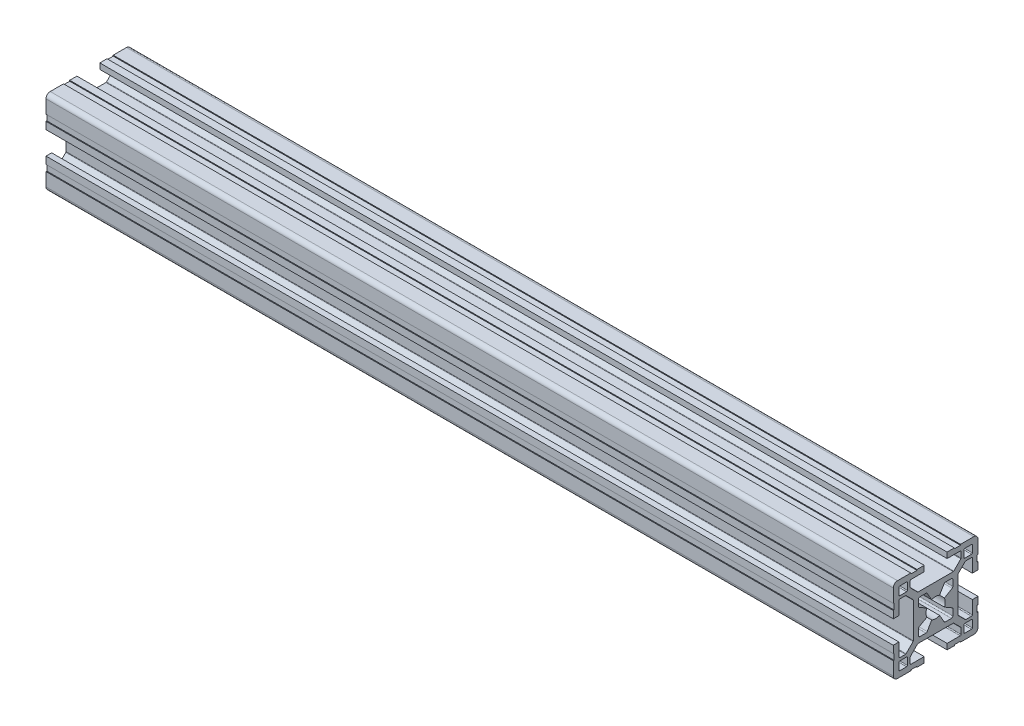
SolidWorks part; units mm, degrees
material "6063-T5"
ref_plane "Plano frontal" through (0, 0, 0) normal (0, 0, 1) x (1, 0, 0)
ref_plane "Plano superior" through (0, 0, 0) normal (0, 1, 0) x (1, 0, 0)
ref_plane "Plano direito" through (0, 0, 0) normal (1, 0, 0) x (0, 0, -1)
sketch "Esboço1" plane through (0, 0, 0) normal (0, 0, 1) x (1, 0, 0)
  line L0 (0, 0) -> (300, 0)
  point P3 (150, 0)
  dimension "D1" = 300
other "Quadrado PF30-11 - PERFIL 3030 CENTRO M8(1)"
ref_plane "Plano1" through (0, 0, 0) normal (1, 0, 0) x (0, 1, 0)
sketch "Sketch1" plane through (0, 0, 0) normal (1, 0, 0) x (0, 1, 0)
  line L0 (-6.1, -3.4254) -> (-6.1, -5.6)
  line L1 (-5.6, -6.1) -> (-3.4254, -6.1)
  line L2 (3.4254, -6.1) -> (5.6, -6.1)
  line L3 (6.1, -5.6) -> (6.1, -3.4254)
  line L4 (6.1, 3.4254) -> (6.1, 5.6)
  line L5 (5.6, 6.1) -> (3.4254, 6.1)
  line L6 (-3.4254, 6.1) -> (-5.6, 6.1)
  line L7 (-6.1, 5.6) -> (-6.1, 3.4254)
  line L8 (15, 6.6) -> (14.7, 6.6)
  line L9 (5.85, -2.9924) -> (3.097, -1.403)
  line L10 (10, 12.7) -> (10, 10.3)
  line L11 (13, -12.7) -> (13, -10.3)
  line L12 (-10.3, -10) -> (-12.7, -10)
  line L13 (-13, 12.7) -> (-13, 10.3)
  line L14 (3.097, 1.403) -> (5.85, 2.9924)
  line L15 (2.9924, 5.85) -> (1.403, 3.097)
  line L16 (-1.403, 3.097) -> (-2.9924, 5.85)
  line L17 (-5.85, 2.9924) -> (-3.097, 1.403)
  line L18 (-3.097, -1.403) -> (-5.85, -2.9924)
  line L19 (-2.9924, -5.85) -> (-1.403, -3.097)
  line L20 (1.403, -3.097) -> (2.9924, -5.85)
  line L21 (10.3, 10) -> (12.7, 10)
  line L22 (13, 10.3) -> (13, 12.7)
  line L23 (12.7, 13) -> (10.3, 13)
  line L24 (12.7, -10) -> (10.3, -10)
  line L25 (10, -10.3) -> (10, -12.7)
  line L26 (10.3, -13) -> (12.7, -13)
  line L27 (-13, -10.3) -> (-13, -12.7)
  line L28 (-12.7, -13) -> (-10.3, -13)
  line L29 (-10, -12.7) -> (-10, -10.3)
  line L30 (-12.7, 10) -> (-10.3, 10)
  line L31 (-10, 10.3) -> (-10, 12.7)
  line L32 (-10.3, 13) -> (-12.7, 13)
  line L33 (15, 4.05) -> (15, 6.6)
  line L34 (13, 4.05) -> (15, 4.05)
  line L35 (13, 8.7) -> (13, 4.05)
  line L36 (10.6799, 9) -> (12.7, 9)
  line L37 (7.9879, 6.4322) -> (10.4678, 8.9121)
  line L38 (7.9, -6.2201) -> (7.9, 6.2201)
  line L39 (10.4678, -8.9121) -> (7.9879, -6.4322)
  line L40 (12.7, -9) -> (10.6799, -9)
  line L41 (13, -4.05) -> (13, -8.7)
  line L42 (15, -4.05) -> (13, -4.05)
  line L43 (15, -6.6) -> (15, -4.05)
  line L44 (14.7, -6.6) -> (15, -6.6)
  line L45 (14.7, -8.8) -> (14.7, -6.6)
  line L46 (15, -8.8) -> (14.7, -8.8)
  line L47 (15, -13.5) -> (15, -8.8)
  line L48 (8.8, -15) -> (13.5, -15)
  line L49 (8.8, -14.7) -> (8.8, -15)
  line L50 (6.6, -14.7) -> (8.8, -14.7)
  line L51 (6.6, -15) -> (6.6, -14.7)
  line L52 (4.05, -15) -> (6.6, -15)
  line L53 (4.05, -13) -> (4.05, -15)
  line L54 (8.7, -13) -> (4.05, -13)
  line L55 (9, -10.6799) -> (9, -12.7)
  line L56 (6.4322, -7.9879) -> (8.9121, -10.4678)
  line L57 (-6.2201, -7.9) -> (6.2201, -7.9)
  line L58 (-8.9121, -10.4678) -> (-6.4322, -7.9879)
  line L59 (-9, -12.7) -> (-9, -10.6799)
  line L60 (-4.05, -13) -> (-8.7, -13)
  line L61 (-4.05, -15) -> (-4.05, -13)
  line L62 (-6.6, -15) -> (-4.05, -15)
  line L63 (-6.6, -14.7) -> (-6.6, -15)
  line L64 (-8.8, -14.7) -> (-6.6, -14.7)
  line L65 (-8.8, -15) -> (-8.8, -14.7)
  line L66 (-13.5, -15) -> (-8.8, -15)
  line L67 (-15, -8.8) -> (-15, -13.5)
  line L68 (-14.7, -8.8) -> (-15, -8.8)
  line L69 (-14.7, -6.6) -> (-14.7, -8.8)
  line L70 (-15, -6.6) -> (-14.7, -6.6)
  line L71 (-15, -4.05) -> (-15, -6.6)
  line L72 (-13, -4.05) -> (-15, -4.05)
  line L73 (-13, -8.7) -> (-13, -4.05)
  line L74 (-10.6799, -9) -> (-12.7, -9)
  line L75 (-7.9879, -6.4322) -> (-10.4678, -8.9121)
  line L76 (-7.9, 6.2201) -> (-7.9, -6.2201)
  line L77 (-10.4678, 8.9121) -> (-7.9879, 6.4322)
  line L78 (-12.7, 9) -> (-10.6799, 9)
  line L79 (-13, 4.05) -> (-13, 8.7)
  line L80 (-15, 4.05) -> (-13, 4.05)
  line L81 (-15, 6.6) -> (-15, 4.05)
  line L82 (-14.7, 6.6) -> (-15, 6.6)
  line L83 (-14.7, 8.8) -> (-14.7, 6.6)
  line L84 (-15, 8.8) -> (-14.7, 8.8)
  line L85 (-15, 13.5) -> (-15, 8.8)
  line L86 (-8.8, 15) -> (-13.5, 15)
  line L87 (-8.8, 14.7) -> (-8.8, 15)
  line L88 (-6.6, 14.7) -> (-8.8, 14.7)
  line L89 (-6.6, 15) -> (-6.6, 14.7)
  line L90 (-4.05, 15) -> (-6.6, 15)
  line L91 (-4.05, 13) -> (-4.05, 15)
  line L92 (-8.7, 13) -> (-4.05, 13)
  line L93 (-9, 10.6799) -> (-9, 12.7)
  line L94 (-6.4322, 7.9879) -> (-8.9121, 10.4678)
  line L95 (6.2201, 7.9) -> (-6.2201, 7.9)
  line L96 (8.9121, 10.4678) -> (6.4322, 7.9879)
  line L97 (9, 12.7) -> (9, 10.6799)
  line L98 (4.05, 13) -> (8.7, 13)
  line L99 (4.05, 15) -> (4.05, 13)
  line L100 (6.6, 15) -> (4.05, 15)
  line L101 (6.6, 14.7) -> (6.6, 15)
  line L102 (8.8, 14.7) -> (6.6, 14.7)
  line L103 (8.8, 15) -> (8.8, 14.7)
  line L104 (13.5, 15) -> (8.8, 15)
  line L105 (15, 8.8) -> (15, 13.5)
  line L106 (14.7, 8.8) -> (15, 8.8)
  line L107 (14.7, 6.6) -> (14.7, 8.8)
  arc A0 (-5.85, -2.9924) -> (-6.1, -3.4254) centre (-5.6, -3.4254) ccw
  arc A1 (-6.1, -5.6) -> (-5.6, -6.1) centre (-5.6, -5.6) ccw
  arc A2 (-3.4254, -6.1) -> (-2.9924, -5.85) centre (-3.4254, -5.6) ccw
  arc A3 (2.9924, -5.85) -> (3.4254, -6.1) centre (3.4254, -5.6) ccw
  arc A4 (5.6, -6.1) -> (6.1, -5.6) centre (5.6, -5.6) ccw
  arc A5 (6.1, -3.4254) -> (5.85, -2.9924) centre (5.6, -3.4254) ccw
  arc A6 (5.85, 2.9924) -> (6.1, 3.4254) centre (5.6, 3.4254) ccw
  arc A7 (6.1, 5.6) -> (5.6, 6.1) centre (5.6, 5.6) ccw
  arc A8 (3.4254, 6.1) -> (2.9924, 5.85) centre (3.4254, 5.6) ccw
  arc A9 (-2.9924, 5.85) -> (-3.4254, 6.1) centre (-3.4254, 5.6) ccw
  arc A10 (-5.6, 6.1) -> (-6.1, 5.6) centre (-5.6, 5.6) ccw
  arc A11 (-6.1, 3.4254) -> (-5.85, 2.9924) centre (-5.6, 3.4254) ccw
  arc A12 (3.097, -1.403) -> (3.097, 1.403) centre (0, 0) ccw
  arc A13 (1.403, 3.097) -> (-1.403, 3.097) centre (0, 0) ccw
  arc A14 (-3.097, 1.403) -> (-3.097, -1.403) centre (0, 0) ccw
  arc A15 (-1.403, -3.097) -> (1.403, -3.097) centre (0, 0) ccw
  arc A16 (10, 10.3) -> (10.3, 10) centre (10.3, 10.3) ccw
  arc A17 (12.7, 10) -> (13, 10.3) centre (12.7, 10.3) ccw
  arc A18 (13, 12.7) -> (12.7, 13) centre (12.7, 12.7) ccw
  arc A19 (10.3, 13) -> (10, 12.7) centre (10.3, 12.7) ccw
  arc A20 (13, -10.3) -> (12.7, -10) centre (12.7, -10.3) ccw
  arc A21 (10.3, -10) -> (10, -10.3) centre (10.3, -10.3) ccw
  arc A22 (10, -12.7) -> (10.3, -13) centre (10.3, -12.7) ccw
  arc A23 (12.7, -13) -> (13, -12.7) centre (12.7, -12.7) ccw
  arc A24 (-12.7, -10) -> (-13, -10.3) centre (-12.7, -10.3) ccw
  arc A25 (-13, -12.7) -> (-12.7, -13) centre (-12.7, -12.7) ccw
  arc A26 (-10.3, -13) -> (-10, -12.7) centre (-10.3, -12.7) ccw
  arc A27 (-10, -10.3) -> (-10.3, -10) centre (-10.3, -10.3) ccw
  arc A28 (-13, 10.3) -> (-12.7, 10) centre (-12.7, 10.3) ccw
  arc A29 (-10.3, 10) -> (-10, 10.3) centre (-10.3, 10.3) ccw
  arc A30 (-10, 12.7) -> (-10.3, 13) centre (-10.3, 12.7) ccw
  arc A31 (-12.7, 13) -> (-13, 12.7) centre (-12.7, 12.7) ccw
  arc A32 (13, 8.7) -> (12.7, 9) centre (12.7, 8.7) ccw
  arc A33 (10.6799, 9) -> (10.4678, 8.9121) centre (10.6799, 8.7) ccw
  arc A34 (7.9879, 6.4322) -> (7.9, 6.2201) centre (8.2, 6.2201) ccw
  arc A35 (7.9, -6.2201) -> (7.9879, -6.4322) centre (8.2, -6.2201) ccw
  arc A36 (10.4678, -8.9121) -> (10.6799, -9) centre (10.6799, -8.7) ccw
  arc A37 (12.7, -9) -> (13, -8.7) centre (12.7, -8.7) ccw
  arc A38 (13.5, -15) -> (15, -13.5) centre (13.5, -13.5) ccw
  arc A39 (8.7, -13) -> (9, -12.7) centre (8.7, -12.7) ccw
  arc A40 (9, -10.6799) -> (8.9121, -10.4678) centre (8.7, -10.6799) ccw
  arc A41 (6.4322, -7.9879) -> (6.2201, -7.9) centre (6.2201, -8.2) ccw
  arc A42 (-6.2201, -7.9) -> (-6.4322, -7.9879) centre (-6.2201, -8.2) ccw
  arc A43 (-8.9121, -10.4678) -> (-9, -10.6799) centre (-8.7, -10.6799) ccw
  arc A44 (-9, -12.7) -> (-8.7, -13) centre (-8.7, -12.7) ccw
  arc A45 (-15, -13.5) -> (-13.5, -15) centre (-13.5, -13.5) ccw
  arc A46 (-13, -8.7) -> (-12.7, -9) centre (-12.7, -8.7) ccw
  arc A47 (-10.6799, -9) -> (-10.4678, -8.9121) centre (-10.6799, -8.7) ccw
  arc A48 (-7.9879, -6.4322) -> (-7.9, -6.2201) centre (-8.2, -6.2201) ccw
  arc A49 (-7.9, 6.2201) -> (-7.9879, 6.4322) centre (-8.2, 6.2201) ccw
  arc A50 (-10.4678, 8.9121) -> (-10.6799, 9) centre (-10.6799, 8.7) ccw
  arc A51 (-12.7, 9) -> (-13, 8.7) centre (-12.7, 8.7) ccw
  arc A52 (-13.5, 15) -> (-15, 13.5) centre (-13.5, 13.5) ccw
  arc A53 (-8.7, 13) -> (-9, 12.7) centre (-8.7, 12.7) ccw
  arc A54 (-9, 10.6799) -> (-8.9121, 10.4678) centre (-8.7, 10.6799) ccw
  arc A55 (-6.4322, 7.9879) -> (-6.2201, 7.9) centre (-6.2201, 8.2) ccw
  arc A56 (6.2201, 7.9) -> (6.4322, 7.9879) centre (6.2201, 8.2) ccw
  arc A57 (8.9121, 10.4678) -> (9, 10.6799) centre (8.7, 10.6799) ccw
  arc A58 (9, 12.7) -> (8.7, 13) centre (8.7, 12.7) ccw
  arc A59 (15, 13.5) -> (13.5, 15) centre (13.5, 13.5) ccw
  point P1 (0, 0)
  point P2 (0, 0)
  point P3 (-15, -15)
  point P4 (0, -15)
  point P5 (-15, 0)
  point P230 (-15, 15)
  point P231 (0, 15)
  point P232 (15, 15)
  point P233 (15, 0)
  point P234 (15, -15)
  point P235 (0, -15)
  point P236 (-15, -15)
  point P237 (-15, 0)
  point P238 (0, 0)
  point P239 (0, 0)
